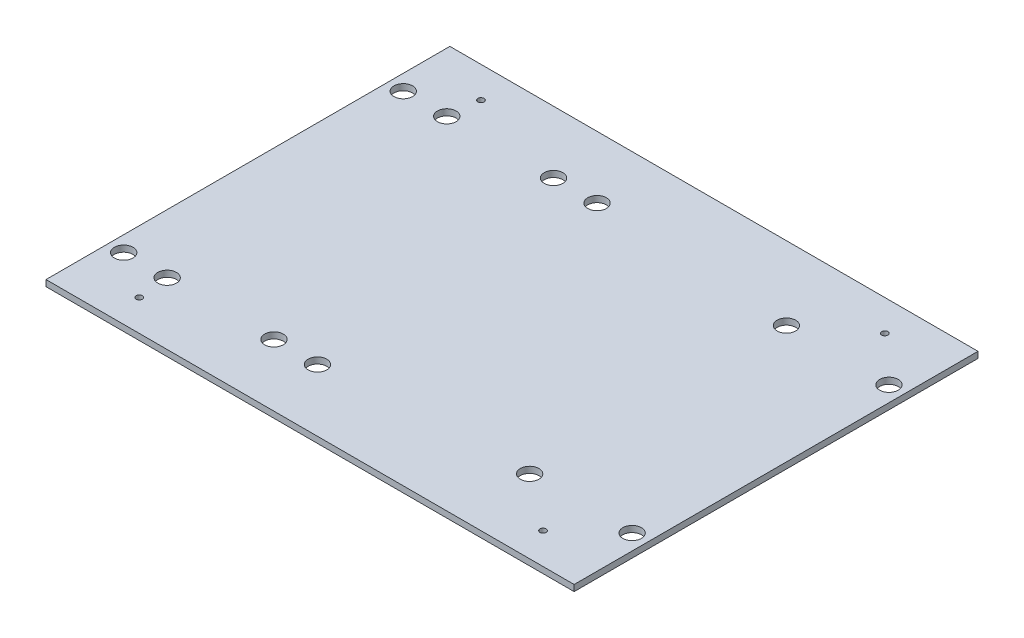
SolidWorks part; units mm, degrees
ref_plane "Front Plane" through (0, 0, 0) normal (0, 0, 1) x (1, 0, 0)
ref_plane "Top Plane" through (0, 0, 0) normal (0, 1, 0) x (1, 0, 0)
ref_plane "Right Plane" through (0, 0, 0) normal (1, 0, 0) x (0, 0, -1)
sketch "Sketch1" plane through (0, 0, 0) normal (0, 1, 0) x (1, 0, 0)
  line L0 (-85, 65) -> (85, -65) construction
  line L1 (-85, 65) -> (85, 65)
  line L2 (-85, 65) -> (-85, -65)
  line L3 (-85, -65) -> (85, -65)
  line L4 (85, 65) -> (85, -65)
  line L5 (-66, 0) -> (-16, 0) construction
  line L6 (-80, 45) -> (-66, 45) construction
  line L7 (-80, 45) -> (-80, -45) construction
  line L8 (-80, -45) -> (-66, -45) construction
  line L9 (-66, 45) -> (-66, -45) construction
  line L10 (-48.8107, 27.1369) -> (-48.8107, -29.0497) construction
  circle A0 centre (-80, 45) radius 3
  circle A1 centre (-66, 45) radius 3
  circle A2 centre (-66, -45) radius 3
  circle A3 centre (-80, -45) radius 3
  circle A4 centre (-31.6214, -45) radius 3
  circle A5 centre (-17.6214, -45) radius 3
  circle A6 centre (-17.6214, 45) radius 3
  circle A7 centre (-31.6214, 45) radius 3
  circle A8 centre (80, 41.33) radius 3
  circle A9 centre (47, 41.33) radius 3
  circle A10 centre (80, -41.33) radius 3
  circle A11 centre (47, -41.33) radius 3
  dimension "D5" = 5
  dimension "D6" = 33
  dimension "D7" = 41.33
  dimension "D9" = 90
  dimension "D1" = 20
  dimension "D2" = 20
  dimension "D3" = 14
  dimension "D4" = 5
  dimension "D8" = 41.33
extrude "Boss-Extrude1" add sketch "Sketch1" along normal blind 2
sketch "Sketch2" plane through (0, 2, 0) normal (0, 1, 0) x (1, 0, 0)
  line L0 (85, -65) -> (85, 65) construction
  line L1 (-85, 65) -> (-85, -65) construction
  line L2 (-65, 55) -> (65, 55) construction
  line L3 (-65, 55) -> (-65, -55) construction
  line L4 (65, 55) -> (65, -55) construction
  line L5 (-65, -55) -> (65, -55) construction
  line L6 (85, 65) -> (-85, 65) construction
  line L8 (-85, -65) -> (85, -65) construction
  circle A0 centre (-65, -55) radius 1
  circle A1 centre (-65, 55) radius 1
  circle A2 centre (65, 55) radius 1
  circle A3 centre (65, -55) radius 1
  dimension "D1" = 10
  dimension "D2" = 20
  dimension "D3" = 20
  dimension "D4" = 10
extrude "Cut-Extrude1" cut sketch "Sketch2" against normal blind 10
